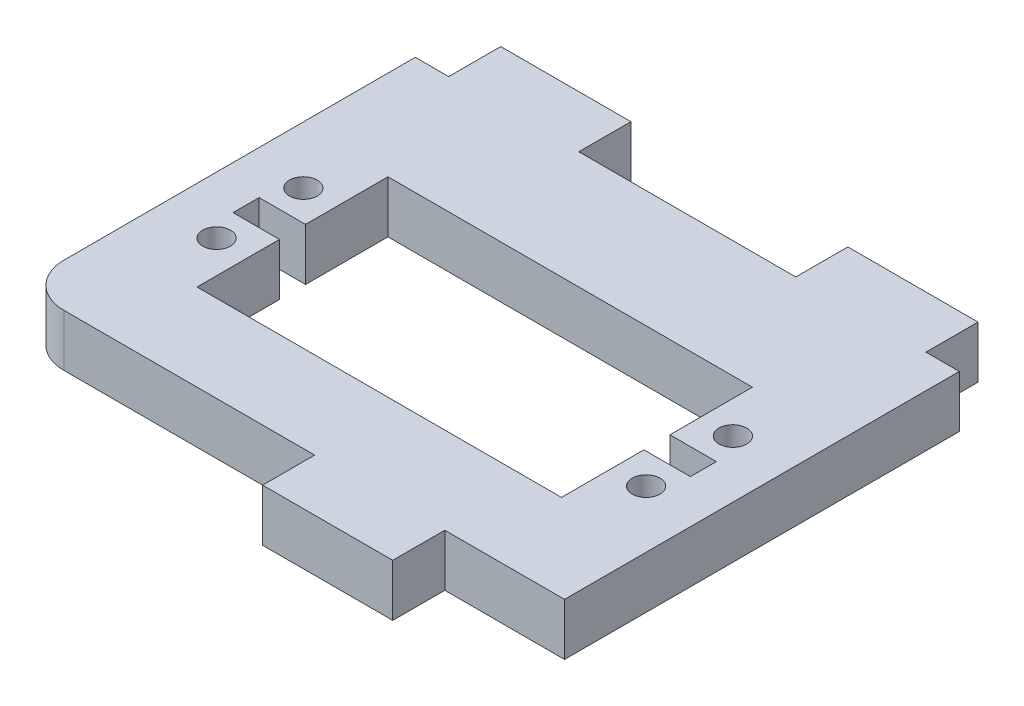
SolidWorks part; units mm, degrees
material "MDF"
ref_plane "Plano frontal" through (0, 0, 0) normal (0, 0, 1) x (1, 0, 0)
ref_plane "Plano superior" through (0, 0, 0) normal (0, 1, 0) x (1, 0, 0)
ref_plane "Plano direito" through (0, 0, 0) normal (1, 0, 0) x (0, 0, -1)
ref_plane "Plano1" through (0, -6, 0) normal (0, -1, 0) x (1, 0, 0)
sketch "Esboço1" plane through (0, -6, 0) normal (0, -1, 0) x (1, 0, 0)
  line L0 (-26.35, 1.5) -> (-21, 1.5)
  line L1 (-21, 1.5) -> (-21, 11)
  line L2 (-21, 11) -> (21, 11)
  line L3 (21, 11) -> (21, 1.5)
  line L4 (21, 1.5) -> (26.35, 1.5)
  line L5 (26.35, 1.5) -> (26.35, -1.5)
  line L6 (26.35, -1.5) -> (21, -1.5)
  line L7 (21, -1.5) -> (21, -11)
  line L8 (21, -11) -> (-21, -11)
  line L9 (-21, -11) -> (-21, -1.5)
  line L10 (-21, -1.5) -> (-26.35, -1.5)
  line L11 (-26.35, -1.5) -> (-26.35, 1.5)
  line L12 (2.5526, 21) -> (-26.35, 21)
  line L13 (-31.35, 16) -> (-31.35, -24.5)
  line L14 (-31.35, -24.5) -> (-27.5, -24.5)
  line L15 (-27.5, -24.5) -> (-27.5, -30.5)
  line L16 (-27.5, -30.5) -> (-12.5, -30.5)
  line L17 (-12.5, -30.5) -> (-12.5, -24.5)
  line L18 (-12.5, -24.5) -> (12.5, -24.5)
  line L19 (12.5, -24.5) -> (12.5, -30.5)
  line L20 (12.5, -30.5) -> (27.5, -30.5)
  line L21 (27.5, -30.5) -> (27.5, -24.5)
  line L22 (27.5, -24.5) -> (31.35, -24.5)
  line L23 (31.35, -24.5) -> (31.35, 21)
  line L24 (31.35, 21) -> (17.5526, 21)
  line L25 (17.5526, 21) -> (17.5526, 27)
  line L26 (17.5526, 27) -> (2.5526, 27)
  line L27 (2.5526, 27) -> (2.5526, 21)
  line L28 (-24.75, 5) -> (24.75, -5) construction
  line L29 (21, 11) -> (-21, -11) construction
  circle A0 centre (24.75, 5) radius 1.6
  circle A1 centre (24.75, -5) radius 1.6
  circle A2 centre (-24.75, 5) radius 1.6
  circle A3 centre (-24.75, -5) radius 1.6
  arc A4 (-26.35, 21) -> (-31.35, 16) centre (-26.35, 16) ccw
  point P38 (0, 0)
  point P46 (0, -24.5)
  point P50 (10.0526, 27)
  point P53 (26.35, 0)
  point P54 (-26.35, 0)
  dimension "D10" = 3.2
  dimension "D11" = 6.6
  dimension "D13" = 5
  dimension "D2" = 62.7
  dimension "D3" = 6
  dimension "D4" = 25
  dimension "D5" = 42
  dimension "D6" = 22
  dimension "D7" = 49.5
  dimension "D8" = 10
  dimension "D9" = 15
  dimension "D12" = 10
  dimension "D14" = 10.0526
  dimension "D15" = 3
  dimension "D16" = 1.6
  dimension "D17" = 13.5
extrude "Ressalto-extrusão1" add sketch "Esboço1" against normal blind 6
